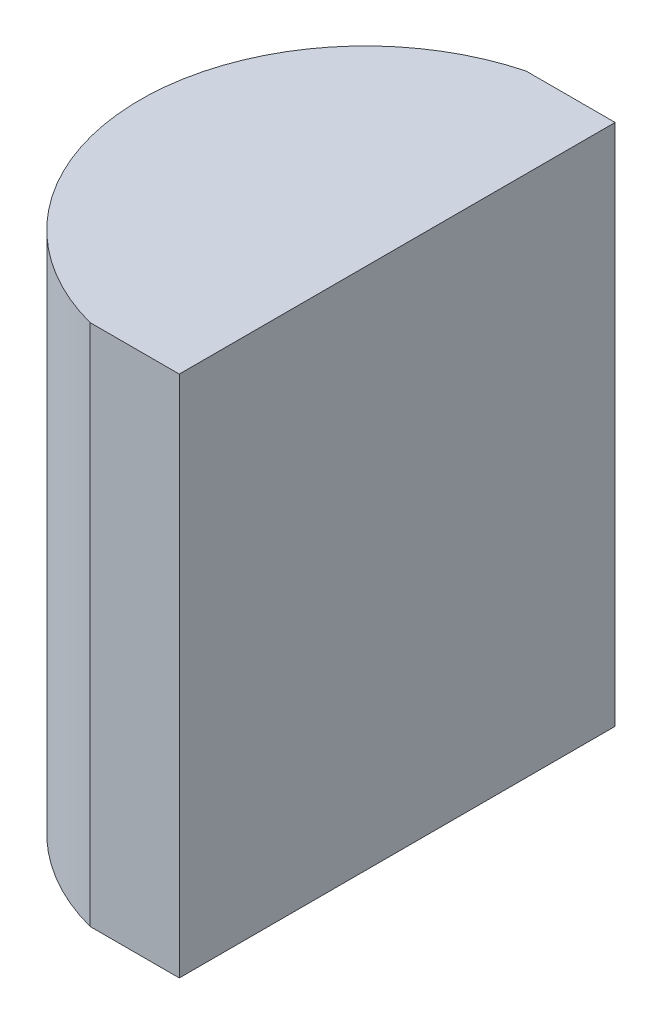
SolidWorks part; units mm, degrees
ref_plane "前视基准面" through (0, 0, 0) normal (0, 0, 1) x (1, 0, 0)
ref_plane "上视基准面" through (0, 0, 0) normal (0, 1, 0) x (1, 0, 0)
ref_plane "右视基准面" through (0, 0, 0) normal (1, 0, 0) x (0, 0, -1)
sketch "草图1" plane through (0, 0, 0) normal (0, 1, 0) x (1, 0, 0)
  line L0 (10.7432, 0) -> (-9.7696, 0) construction
  line L1 (3.0403, 5) -> (5.0852, 5)
  line L2 (3.0403, -5) -> (5.0852, -5)
  line L3 (5.0852, 5) -> (5.0852, -5)
  arc A0 (3.0403, 5) -> (3.0403, -5) centre (4.3552, 0) ccw
  point P19 (-0.8148, 0)
  point P20 (5.0852, 0)
  dimension "D2" = 5
  dimension "D3" = 5.17
  dimension "D4" = 5.9
  dimension "D1" = 5
extrude "凸台-拉伸1" add sketch "草图1" along normal blind 12
